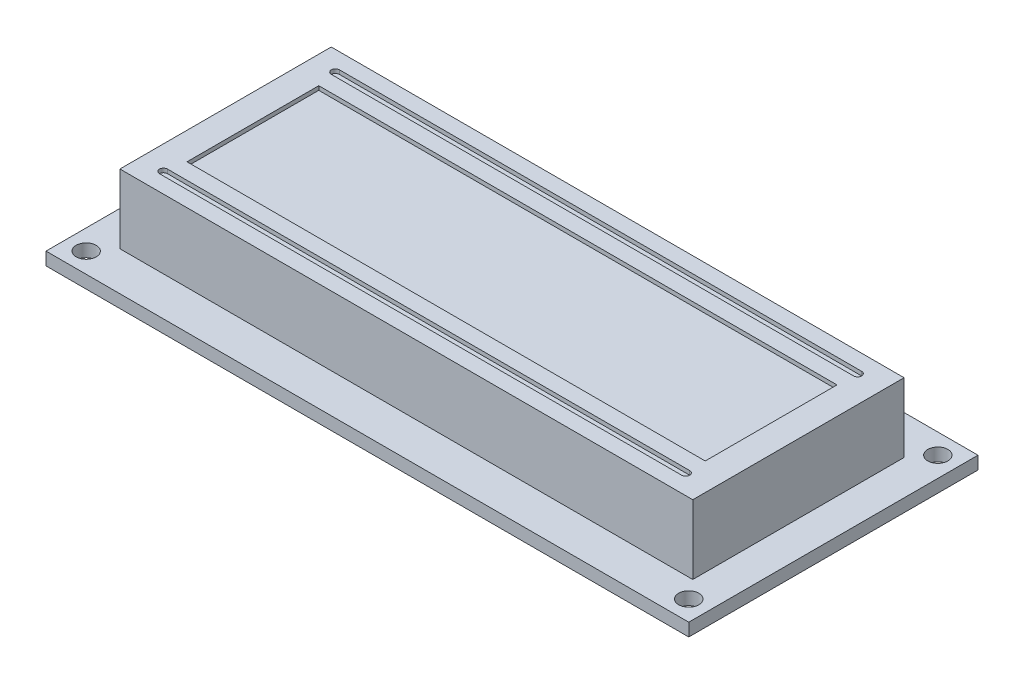
SolidWorks part; units mm, degrees
ref_plane "Front Plane" through (0, 0, 0) normal (0, 0, 1) x (1, 0, 0)
ref_plane "Top Plane" through (0, 0, 0) normal (0, 1, 0) x (1, 0, 0)
ref_plane "Right Plane" through (0, 0, 0) normal (1, 0, 0) x (0, 0, -1)
sketch "Sketch1" plane through (0, 0, 0) normal (0, 1, 0) x (1, 0, 0)
  line L1 (40, -18) -> (-40, -18)
  line L2 (40, -18) -> (40, 18)
  line L3 (40, 18) -> (-40, 18)
  line L4 (-40, -18) -> (-40, 18)
  line L5 (40, -18) -> (-40, 18) construction
  line L6 (40, 18) -> (-40, -18) construction
  circle A0 centre (-37.5, 15.5) radius 1.25
  circle A1 centre (37.5, 15.5) radius 1.25
  circle A2 centre (37.5, -15.5) radius 1.25
  circle A3 centre (-37.5, -15.5) radius 1.25
  circle A4 centre (-32, 16.25) radius 0.5
  circle A5 centre (-29.46, 16.25) radius 0.5
  circle A6 centre (-26.92, 16.25) radius 0.5
  circle A7 centre (-24.38, 16.25) radius 0.5
  circle A8 centre (-21.84, 16.25) radius 0.5
  circle A9 centre (-19.3, 16.25) radius 0.5
  circle A10 centre (-16.76, 16.25) radius 0.5
  circle A11 centre (-14.22, 16.25) radius 0.5
  circle A12 centre (-11.68, 16.25) radius 0.5
  circle A13 centre (-9.14, 16.25) radius 0.5
  circle A14 centre (-6.6, 16.25) radius 0.5
  circle A15 centre (-4.06, 16.25) radius 0.5
  circle A16 centre (-1.52, 16.25) radius 0.5
  circle A17 centre (1.02, 16.25) radius 0.5
  circle A18 centre (3.56, 16.25) radius 0.5
  circle A19 centre (6.1, 16.25) radius 0.5
  point P0 (0, 0)
  dimension "D3" = 2.5
  dimension "D12" = 1
  dimension "D1" = 80
  dimension "D2" = 36
  dimension "D4" = 2.5
  dimension "D5" = 2.5
  dimension "D6" = 2.5
  dimension "D7" = 2.5
  dimension "D8" = 2.5
  dimension "D9" = 2.5
  dimension "D10" = 2.5
  dimension "D11" = 2.5
  dimension "D13" = 8
  dimension "D14" = 1.75
  dimension "D15" = 16
extrude "Boss-Extrude1" add sketch "Sketch1" along normal blind 1.6
sketch "Sketch2" plane through (0, 1.6, 0) normal (0, 1, 0) x (1, 0, 0)
  line L1 (35.65, -13.15) -> (-35.65, -13.15)
  line L2 (35.65, -13.15) -> (35.65, 13.15)
  line L3 (35.65, 13.15) -> (-35.65, 13.15)
  line L4 (-35.65, -13.15) -> (-35.65, 13.15)
  line L5 (35.65, -13.15) -> (-35.65, 13.15) construction
  line L6 (35.65, 13.15) -> (-35.65, -13.15) construction
  point P0 (0, 0)
  dimension "D1" = 71.3
  dimension "D2" = 26.3
extrude "Boss-Extrude2" add sketch "Sketch2" along normal blind 8.6
sketch "Sketch3" plane through (0, 10.2, 0) normal (0, 1, 0) x (1, 0, 0)
  line L1 (32.25, -8.2) -> (-32.25, -8.2)
  line L2 (32.25, -8.2) -> (32.25, 8.2)
  line L3 (32.25, 8.2) -> (-32.25, 8.2)
  line L4 (-32.25, -8.2) -> (-32.25, 8.2)
  line L5 (32.25, -8.2) -> (-32.25, 8.2) construction
  line L6 (32.25, 8.2) -> (-32.25, -8.2) construction
  point P0 (0, 0)
  dimension "D1" = 16.4
  dimension "D2" = 64.5
extrude "Cut-Extrude1" cut sketch "Sketch3" against normal blind 0.5
sketch "Sketch4" plane through (0, 10.2, 0) normal (0, 1, 0) x (1, 0, 0)
  line L0 (-32.6815, 10.7) -> (32.3185, 10.7) construction
  line L6 (32.25, 8.2) -> (-32.25, 8.2) construction
  line L11 (-32.6815, 10.2) -> (32.3185, 10.2)
  line L12 (-32.6815, 11.2) -> (32.3185, 11.2)
  arc A2 (-32.6815, 10.2) -> (-32.6815, 11.2) centre (-32.6815, 10.7) cw
  arc A3 (32.3185, 10.2) -> (32.3185, 11.2) centre (32.3185, 10.7) ccw
  dimension "D1" = 2.5
  dimension "D2" = 0.5
  dimension "D4" = 65
  dimension "D3" = 0.5
extrude "Cut-Extrude2" cut sketch "Sketch4" against normal blind 0.5
mirror "Mirror1" about plane through (0, 0, 0) normal (0, 0, 1) of "Cut-Extrude2"
sketch "Sketch5" plane through (0, 0, 0) normal (0, -1, 0) x (1, 0, 0)
  line L1 (-33.27, -14.98) -> (7.37, -14.98)
  line L2 (-33.27, -14.98) -> (-33.27, -17.52)
  line L3 (-33.27, -17.52) -> (7.37, -17.52)
  line L4 (7.37, -14.98) -> (7.37, -17.52)
  circle A0 centre (-32, -16.25) radius 0.5 construction
  circle A1 centre (6.1, -16.25) radius 0.5 construction
  dimension "D1" = 2.54
  dimension "D2" = 1.27
  dimension "D3" = 1.27
  dimension "D4" = 1.27
extrude "Boss-Extrude3" add sketch "Sketch5" along normal blind 2.54
sketch "Sketch6" plane through (0, -2.54, 0) normal (0, -1, 0) x (1, 0, 0)
  circle A0 centre (-32, -16.25) radius 0.5
  circle A1 centre (-29.46, -16.25) radius 0.5
  circle A2 centre (-26.92, -16.25) radius 0.5
  circle A3 centre (-24.38, -16.25) radius 0.5
  circle A4 centre (-21.84, -16.25) radius 0.5
  circle A5 centre (-19.3, -16.25) radius 0.5
  circle A6 centre (-16.76, -16.25) radius 0.5
  circle A7 centre (-14.22, -16.25) radius 0.5
  circle A8 centre (-11.68, -16.25) radius 0.5
  circle A9 centre (-9.14, -16.25) radius 0.5
  circle A10 centre (-6.6, -16.25) radius 0.5
  circle A11 centre (-4.06, -16.25) radius 0.5
  circle A12 centre (-1.52, -16.25) radius 0.5
  circle A13 centre (1.02, -16.25) radius 0.5
  circle A14 centre (3.56, -16.25) radius 0.5
  circle A15 centre (6.1, -16.25) radius 0.5
  dimension "D1" = 16
extrude "Boss-Extrude4" add sketch "Sketch6" along normal blind 11.5 and the other way blind 4.54
sketch "Sketch7" plane through (0, -2.54, 0) normal (0, -1, 0) x (1, 0, 0)
  line L1 (-33.27, -14.98) -> (7.37, -14.98)
  line L2 (-33.27, -14.98) -> (-33.27, -17.52)
  line L3 (-33.27, -17.52) -> (7.37, -17.52)
  line L4 (7.37, -14.98) -> (7.37, -17.52)
extrude "Boss-Extrude5" add sketch "Sketch7" along normal blind 8.5
equation "\"D6@Sketch1\"=\"D5@Sketch1\""
equation "\"D7@Sketch1\"=\"D4@Sketch1\""
equation "\"D8@Sketch1\"=\"D3@Sketch1\""
equation "\"D9@Sketch1\"=\"D3@Sketch1\""
equation "\"D10@Sketch1\"=\"D4@Sketch1\""
equation "\"D11@Sketch1\"=\"D4@Sketch1\""
equation "\"D2@Sketch5\"=2.54/2"
equation "\"D3@Sketch5\"=2.54/2"
equation "\"D4@Sketch5\"=2.54/2"
